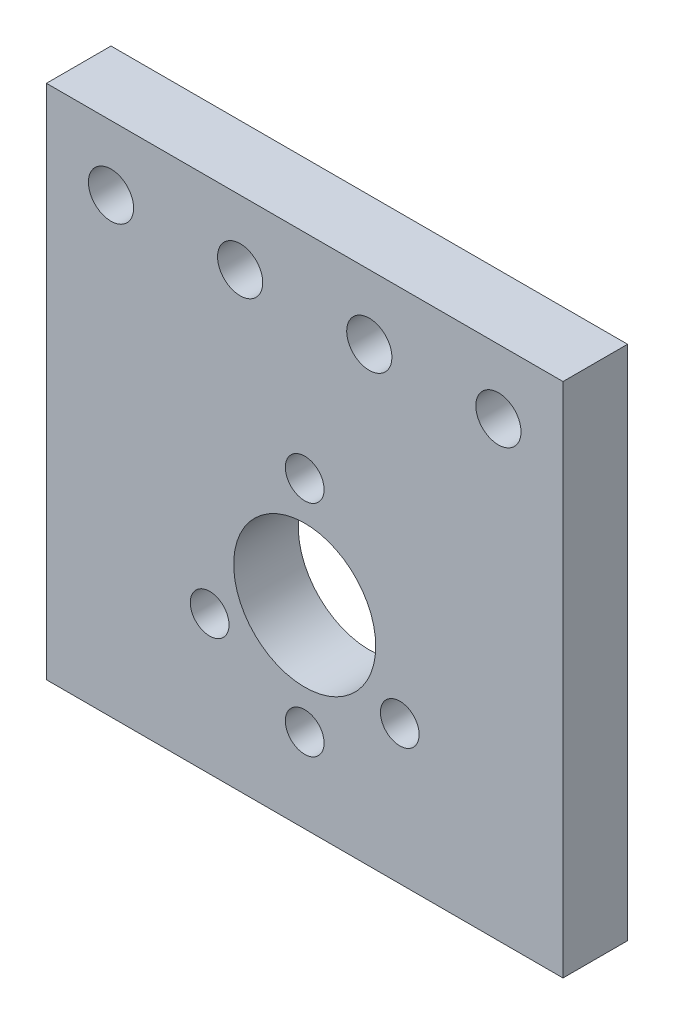
SolidWorks part; units mm, degrees
ref_plane "Front Plane" through (0, 0, 0) normal (0, 0, 1) x (1, 0, 0)
ref_plane "Top Plane" through (0, 0, 0) normal (0, 1, 0) x (1, 0, 0)
ref_plane "Right Plane" through (0, 0, 0) normal (1, 0, 0) x (0, 0, -1)
sketch "Sketch1" plane through (0, 0, 0) normal (0, 0, 1) x (1, 0, 0)
  line L0 (0, 0) -> (0, -30.9437) construction
  line L1 (0, 0) -> (26.8972, -15.5291) construction
  line L3 (-20, 25) -> (20, 25)
  line L4 (-20, 25) -> (-20, -15)
  line L5 (-20, -15) -> (20, -15)
  line L6 (20, 25) -> (20, -15)
  circle A0 centre (0, 0) radius 5.5
  circle A1 centre (0, -8.5) radius 1.5
  circle A2 centre (0, 8.5) radius 1.5
  circle A3 centre (7.3612, -4.25) radius 1.5
  circle A4 centre (-7.3612, -4.25) radius 1.5
  circle A5 centre (-15, 20) radius 1.75
  circle A6 centre (-5, 20) radius 1.75
  circle A7 centre (5, 20) radius 1.75
  circle A8 centre (15, 20) radius 1.75
  dimension "D1" = 8.5
  dimension "D2" = 8.5
  dimension "D5" = 20
  dimension "D7" = 5
  dimension "D9" = 10
  dimension "D3" = 60
  dimension "D4" = 8.5
  dimension "D6" = 25
  dimension "D8" = 5
extrude "Boss-Extrude1" add sketch "Sketch1" along normal blind 5
